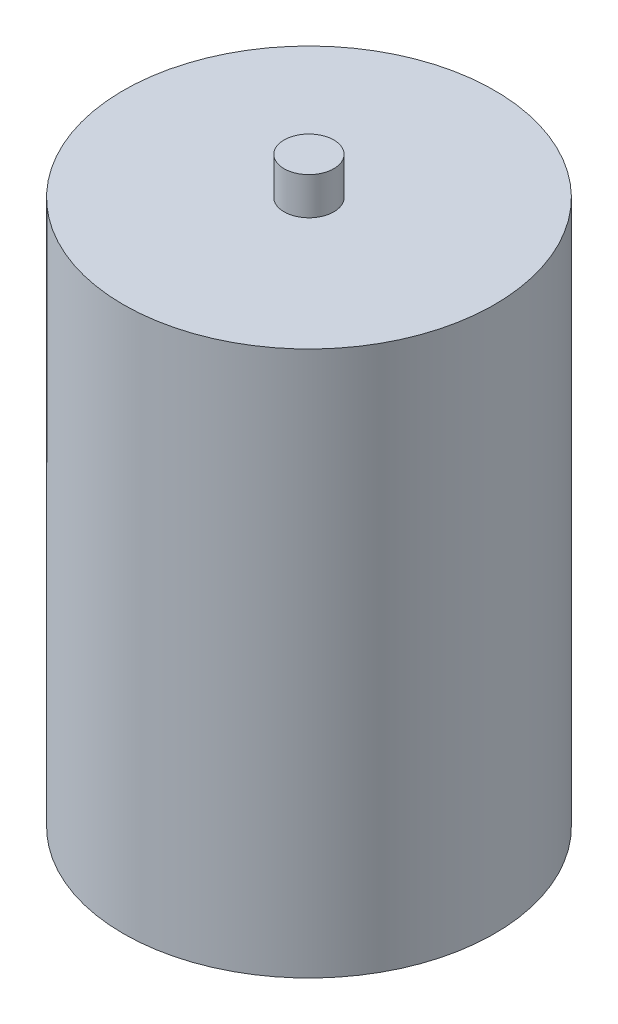
SolidWorks part; units mm, degrees
ref_plane "Front Plane" through (0, 0, 0) normal (0, 0, 1) x (1, 0, 0)
ref_plane "Top Plane" through (0, 0, 0) normal (0, 1, 0) x (1, 0, 0)
ref_plane "Right Plane" through (0, 0, 0) normal (1, 0, 0) x (0, 0, -1)
sketch "Sketch1" plane through (0, 0, 0) normal (0, 1, 0) x (1, 0, 0)
  circle A0 centre (0, 0) radius 125.984
extrude "Boss-Extrude1" add sketch "Sketch1" along normal blind 369.824
sketch "Sketch2" plane through (0, 369.824, 0) normal (0, 1, 0) x (1, 0, 0)
  circle A0 centre (0, 0) radius 16.891
extrude "Boss-Extrude2" add sketch "Sketch2" along normal blind 25.4
sketch "Sketch3" plane through (0, 369.824, 0) normal (0, 1, 0) x (1, 0, 0)
  line L1 (-125.984, -125.984) -> (125.984, -125.984)
  line L2 (-125.984, -125.984) -> (-125.984, 210.058)
  line L3 (-125.984, 210.058) -> (125.984, 210.058)
  line L4 (125.984, -125.984) -> (125.984, 210.058)
